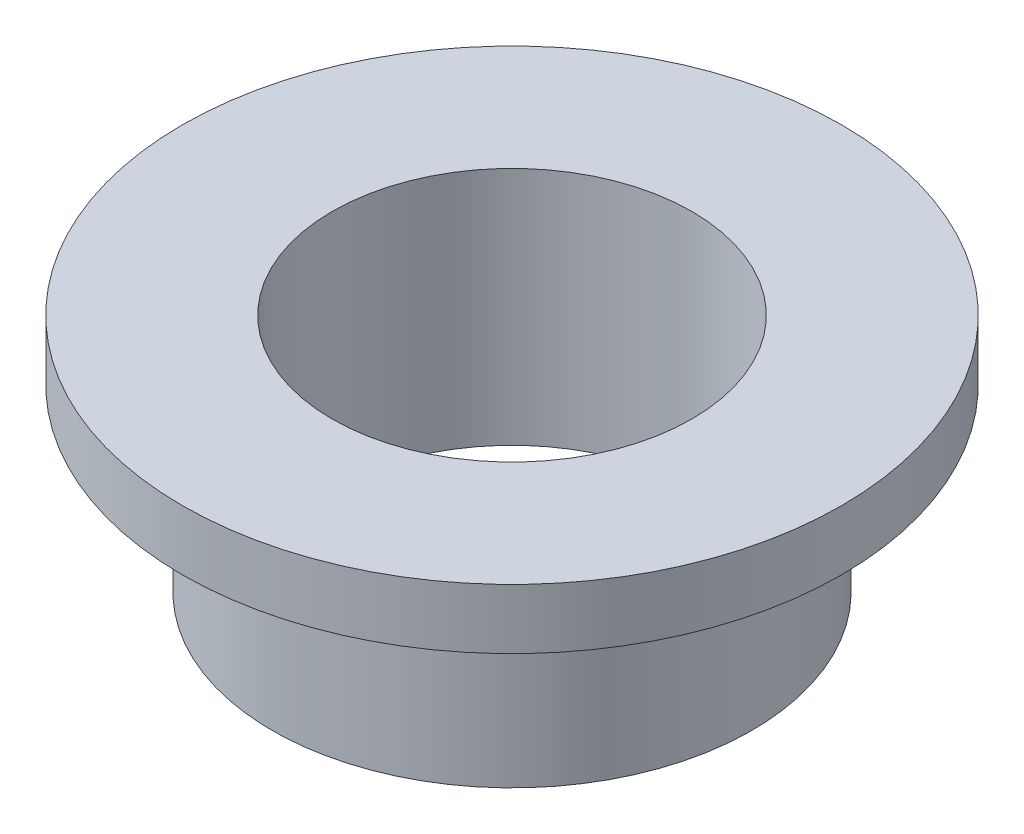
SolidWorks part; units mm, degrees
material "Leaded Commercial Bronze"
ref_plane "Front Plane" through (0, 0, 0) normal (0, 0, 1) x (1, 0, 0)
ref_plane "Top Plane" through (0, 0, 0) normal (0, 1, 0) x (1, 0, 0)
ref_plane "Right Plane" through (0, 0, 0) normal (1, 0, 0) x (0, 0, -1)
ref_axis "Axis1" through (0, -55, 0) along (0, 1, 0)
sketch "Sketch1" plane through (0, 0, 0) normal (0, 0, 1) x (1, 0, 0)
  line L0 (4.7625, -11.6384) -> (8.7313, -11.6384)
  line L1 (8.7313, -11.6384) -> (8.7313, -13.2259)
  line L2 (8.7313, -13.2259) -> (6.35, -13.2259)
  line L3 (6.35, -13.2259) -> (6.35, -17.9884)
  line L4 (6.35, -17.9884) -> (4.7625, -17.9884)
  line L5 (4.7625, -17.9884) -> (4.7625, -11.6384)
  line L6 (0, -55) -> (0, 55) construction
  dimension "D1" = 4.7625
  dimension "D2" = 6.35
  dimension "D3" = 1.5875
  dimension "D4" = 8.7312
  dimension "D5" = 6.35
revolve "Revolve1" add sketch "Sketch1" angle 360 about axis through (0, -55, 0) along (0, 1, 0)
